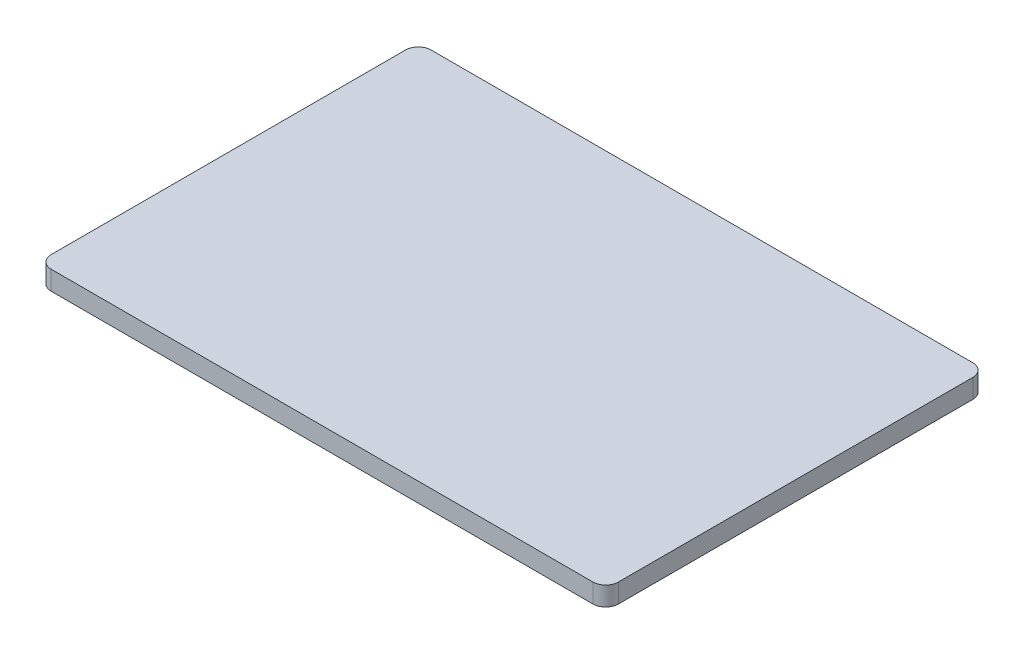
SolidWorks part; units mm, degrees
ref_plane "Front Plane" through (0, 0, 0) normal (0, 0, 1) x (1, 0, 0)
ref_plane "Top Plane" through (0, 0, 0) normal (0, 1, 0) x (1, 0, 0)
ref_plane "Right Plane" through (0, 0, 0) normal (1, 0, 0) x (0, 0, -1)
sketch "Sketch1" plane through (0, 0, 0) normal (0, 1, 0) x (1, 0, 0)
  line L1 (-44.5196, 29.813) -> (44.5196, 29.813)
  line L2 (-44.5196, 29.813) -> (-44.5196, -29.813)
  line L3 (-44.5196, -29.813) -> (44.5196, -29.813)
  line L4 (44.5196, 29.813) -> (44.5196, -29.813)
  line L5 (-44.5196, 29.813) -> (44.5196, -29.813) construction
  line L6 (-44.5196, -29.813) -> (44.5196, 29.813) construction
  point P0 (0, 0)
  dimension "D1" = 89.0392
  dimension "D2" = 59.626
extrude "Boss-Extrude1" add sketch "Sketch1" along normal blind 2.9972
fillet "Fillet1" radius 2 4 edges at (-44.5196, 1.4986, 29.813) (-44.5196, 1.4986, -29.813) (44.5196, 1.4986, -29.813) (44.5196, 1.4986, 29.813)
